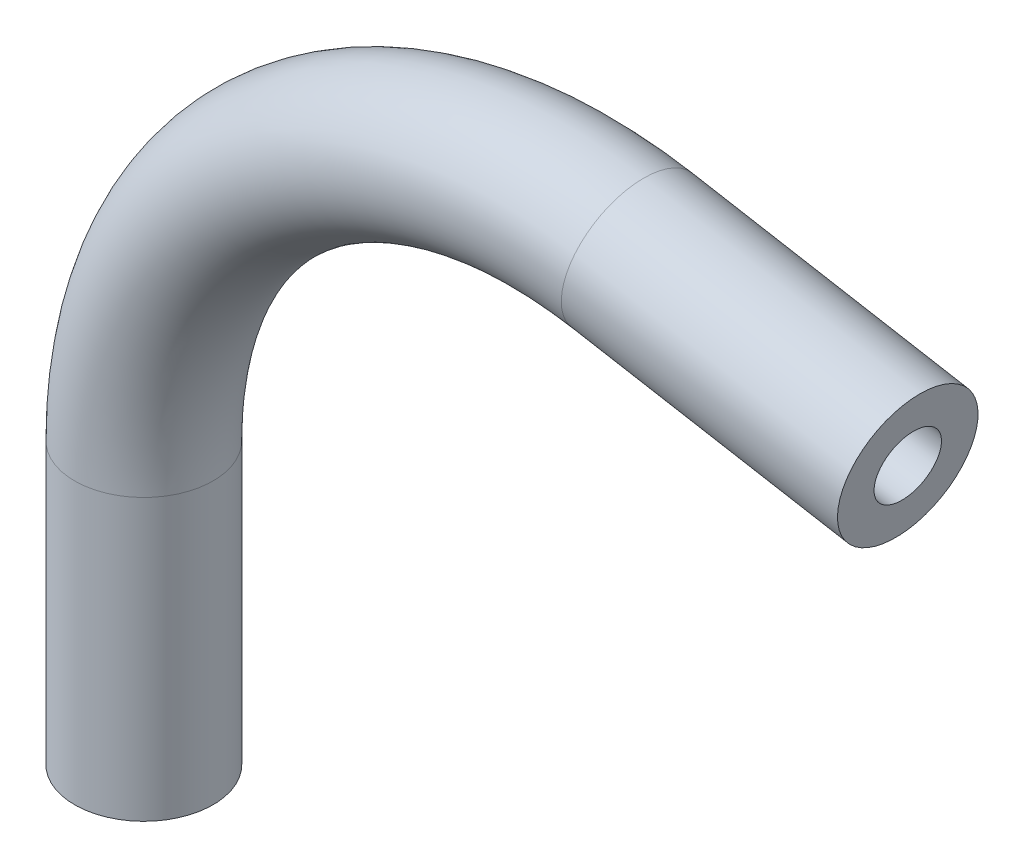
SolidWorks part; units mm, degrees
material "6061 Alloy"
ref_plane "Front Plane" through (0, 0, 0) normal (0, 0, 1) x (1, 0, 0)
ref_plane "Top Plane" through (0, 0, 0) normal (0, 1, 0) x (1, 0, 0)
ref_plane "Right Plane" through (0, 0, 0) normal (1, 0, 0) x (0, 0, -1)
sketch "Sketch1" plane through (0, 0, 0) normal (0, 0, 1) x (1, 0, 0)
  line L0 (0, -14.3794) -> (0, -1.5223)
  line L1 (22.358, 17.2383) -> (35.0198, 15.0057)
  arc A0 (0, -1.5223) -> (22.358, 17.2383) centre (19.05, -1.5223) cw
  point P6 (0, 21.1806)
  dimension "D3" = 19.05
  dimension "D1" = 35.56
  dimension "D2" = 35.56
  dimension "D4" = 100
ref_plane "Plane1" through (35.0198, 15.0057, 0) normal (0.9848, -0.1736, 0) x (0, 0, -1)
sketch "Sketch2" plane through (35.0198, 15.0057, 0) normal (0.9848, -0.1736, 0) x (0, 0, -1)
  circle A0 centre (0, 0) radius 3.175
  circle A1 centre (0, 0) radius 1.524
  dimension "D1" = 6.35
  dimension "D2" = 3.048
sweep "Sweep1" add profiles "Sketch2" path "Sketch1"
